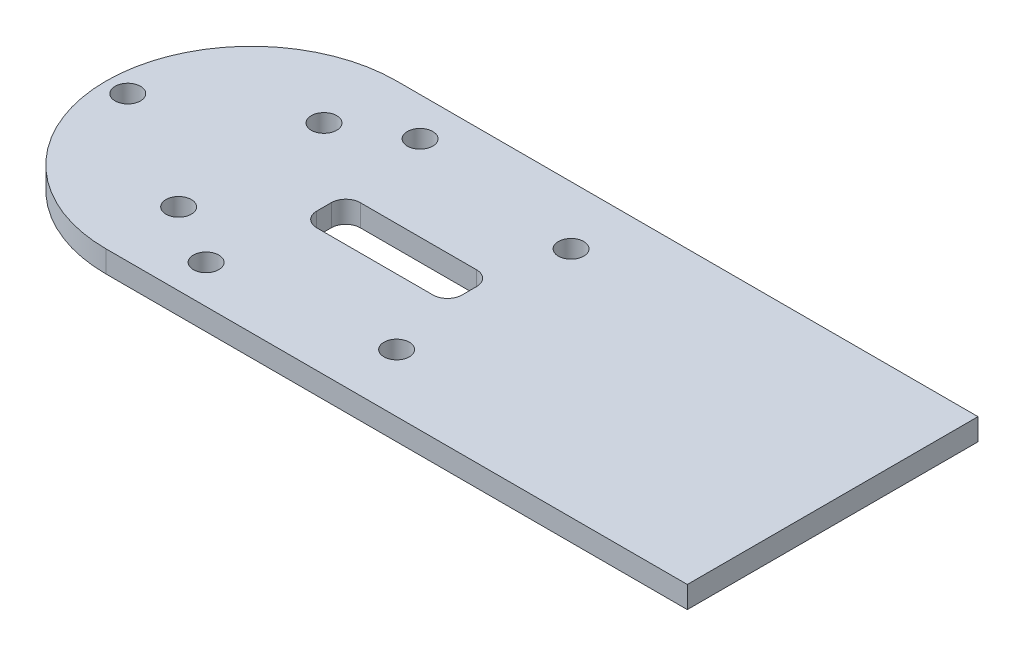
SolidWorks part; units mm, degrees
ref_plane "Front" through (0, 0, 0) normal (0, 0, 1) x (1, 0, 0)
ref_plane "Top" through (0, 0, 0) normal (0, 1, 0) x (1, 0, 0)
ref_plane "Right" through (0, 0, 0) normal (1, 0, 0) x (0, 0, -1)
sketch "Sketch1" plane through (0, 0, 0) normal (0, 1, 0) x (1, 0, 0)
  line L1 (50, -20) -> (-30, -20)
  line L2 (50, -20) -> (50, 20)
  line L3 (50, 20) -> (-30, 20)
  line L5 (50, -20) -> (0, 0) construction
  line L6 (50, 20) -> (0, 0) construction
  arc A0 (-30, 20) -> (-30, -20) centre (-30, 0) ccw
  point P0 (0, 0)
  dimension "D3" = 40
extrude "Boss-Extrude1" add sketch "Sketch1" along normal blind 3
sketch "Sketch2" plane through (0, 3, 0) normal (0, 1, 0) x (1, 0, 0)
  line L0 (-50, 0) -> (50, 0) construction
  line L2 (50, -20) -> (50, 20) construction
  circle A0 centre (-30, 0) radius 12.5 construction
  dimension "D1" = 25
  dimension "D2" = 20
  dimension "D3" = 20
sketch "Sketch3" plane through (0, 3, 0) normal (0, 1, 0) x (1, 0, 0)
  line L0 (-50, 0) -> (50, 0) construction
  circle A0 centre (-30, 10) radius 1.75
  circle A1 centre (-30, -10) radius 1.75
  dimension "D1" = 3.5
  dimension "D2" = 3.5
  dimension "D3" = 10
  dimension "D4" = 10
  dimension "D5" = 20
  dimension "D6" = 20
extrude "Cut-Extrude1" cut sketch "Sketch3" against normal through all
sketch "Sketch4" plane through (0, 0, 0) normal (0, -1, 0) x (1, 0, 0)
  line L0 (-50, 0) -> (50, 0) construction
  line L1 (0, -3) -> (-20, -3)
  line L2 (0, -3) -> (0, 3)
  line L3 (0, 3) -> (-20, 3)
  line L4 (-20, -3) -> (-20, 3)
  line L5 (0, -3) -> (-20, 3) construction
  line L6 (0, 3) -> (-20, -3) construction
  line L7 (-20, -7.5) -> (-20, 7.5) construction
  point P0 (-10, 0)
  dimension "D1" = 20
  dimension "D2" = 6
extrude "Cut-Extrude2" cut sketch "Sketch4" against normal up to next
fillet "Fillet1" radius 2 4 edges at (-20, 1.5, -3) (-20, 1.5, 3) (0, 1.5, -3) (0, 1.5, 3)
sketch "Sketch5" plane through (0, 0, 0) normal (0, -1, 0) x (1, 0, 0)
  circle A0 centre (-21.5, -14.7224) radius 1.75
  circle A1 centre (-21.5, 14.7224) radius 1.75
  circle A2 centre (-47, 0) radius 1.75
extrude "Cut-Extrude3" cut sketch "Sketch5" against normal up to next
sketch "Sketch6" plane through (0, 3, 0) normal (0, 1, 0) x (-1, 0, 0)
  line L0 (-10, -20) -> (-10, 20) construction
  line L1 (-50, -20) -> (30, -20) construction
  line L2 (30, 20) -> (-50, 20) construction
  line L3 (-50, 20) -> (-50, -20) construction
  dimension "D1" = 40
sketch "Sketch7" plane through (0, 0, 0) normal (0, -1, 0) x (1, 0, 0)
  line L0 (10, -20) -> (10, 20) construction
  line L1 (50, -20) -> (-30, -20) construction
  line L2 (-30, 20) -> (50, 20) construction
  circle A0 centre (2, 12) radius 1.75
  circle A1 centre (2, -12) radius 1.75
  dimension "D1" = 3.5
  dimension "D2" = 3.5
  dimension "D3" = 8
  dimension "D4" = 8
  dimension "D5" = 8
  dimension "D6" = 8
extrude "Cut-Extrude4" cut sketch "Sketch7" against normal up to next
